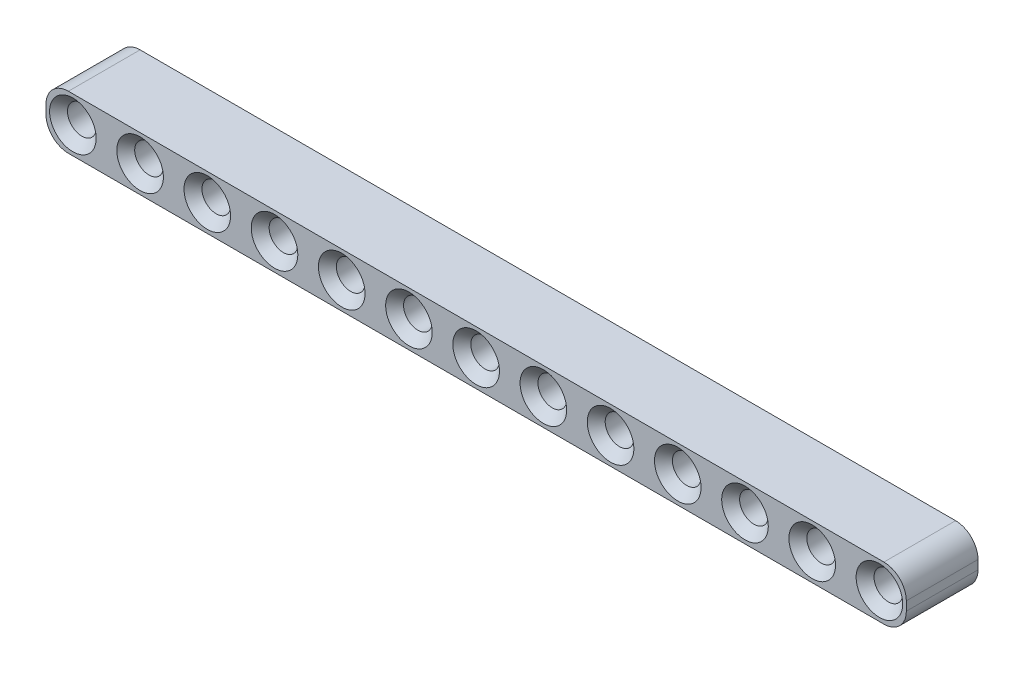
SolidWorks part; units mm, degrees
ref_plane "Front Plane" through (0, 0, 0) normal (0, 0, 1) x (1, 0, 0)
ref_plane "Top Plane" through (0, 0, 0) normal (0, 1, 0) x (1, 0, 0)
ref_plane "Right Plane" through (0, 0, 0) normal (1, 0, 0) x (0, 0, -1)
sketch "Sketch1" plane through (0, 0, 0) normal (0, 0, 1) x (1, 0, 0)
  line L1 (-0.5, 3) -> (90.5, 3)
  line L2 (-3, 0.5) -> (-3, -0.5)
  line L3 (-0.5, -3) -> (90.5, -3)
  line L4 (93, 0.5) -> (93, -0.5)
  circle A0 centre (0, 0) radius 1.6
  arc A1 (90.5, -3) -> (93, -0.5) centre (90.5, -0.5) ccw
  arc A2 (90.5, 3) -> (93, 0.5) centre (90.5, 0.5) cw
  arc A3 (-3, -0.5) -> (-0.5, -3) centre (-0.5, -0.5) ccw
  arc A4 (-0.5, 3) -> (-3, 0.5) centre (-0.5, 0.5) ccw
  circle A5 centre (7.5, 0) radius 1.6
  circle A6 centre (15, 0) radius 1.6
  circle A7 centre (22.5, 0) radius 1.6
  circle A8 centre (30, 0) radius 1.6
  circle A9 centre (37.5, 0) radius 1.6
  circle A10 centre (45, 0) radius 1.6
  circle A11 centre (52.5, 0) radius 1.6
  circle A12 centre (60, 0) radius 1.6
  circle A13 centre (67.5, 0) radius 1.6
  circle A14 centre (75, 0) radius 1.6
  circle A15 centre (82.5, 0) radius 1.6
  circle A16 centre (90, 0) radius 1.6
  point P8 (-3, 0)
  point P14 (-3, -3)
  point P17 (-3, 3)
  dimension "D1" = 3.2
  dimension "D4" = 2.5
  dimension "D2" = 6
  dimension "D3" = 3
  dimension "D6" = 7.5
  dimension "D5" = 13
extrude "Boss-Extrude1" add sketch "Sketch1" along normal blind 8
chamfer "Chamfer1" distance 1 angle 45 26 edges at (84.1, 0, 0) (84.1, 0, 8) (91.6, 0, 0) (91.6, 0, 8) (76.6, 0, 0) (76.6, 0, 8) (69.1, 0, 0) (69.1, 0, 8) (61.6, 0, 0) (61.6, 0, 8) (54.1, 0, 0) (54.1, 0, 8) (46.6, 0, 0) (46.6, 0, 8) (39.1, 0, 0) (39.1, 0, 8) (31.6, 0, 0) (31.6, 0, 8) (24.1, 0, 0) (24.1, 0, 8) (16.6, 0, 0) (16.6, 0, 8) (9.1, 0, 0) (9.1, 0, 8) (1.6, 0, 0) (1.6, 0, 8)
